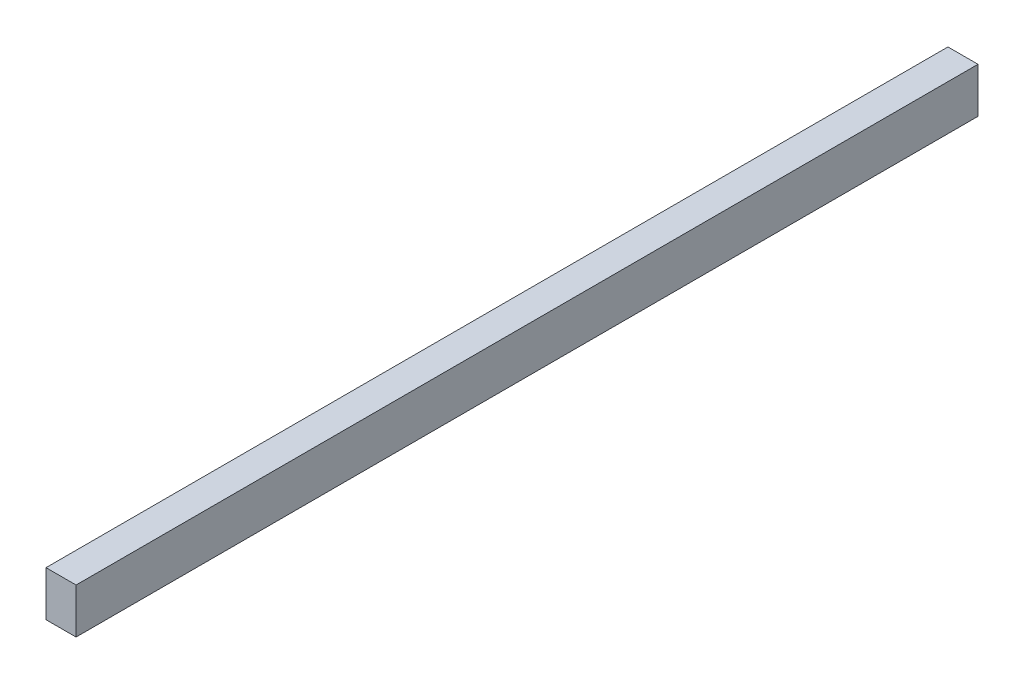
SolidWorks part; units mm, degrees
ref_plane "Спереди" through (0, 0, 0) normal (0, 0, 1) x (1, 0, 0)
ref_plane "Сверху" through (0, 0, 0) normal (0, 1, 0) x (1, 0, 0)
ref_plane "Справа" through (0, 0, 0) normal (1, 0, 0) x (0, 0, -1)
sketch "Эскиз1" plane through (0, 0, 0) normal (0, 0, 1) x (1, 0, 0)
  line L1 (0, 0) -> (10, 0)
  line L2 (0, 0) -> (0, 15)
  line L3 (0, 15) -> (10, 15)
  line L4 (10, 0) -> (10, 15)
  dimension "D1" = 10
  dimension "D2" = 15
extrude "Бобышка-Вытянуть1" add sketch "Эскиз1" along normal blind 300
